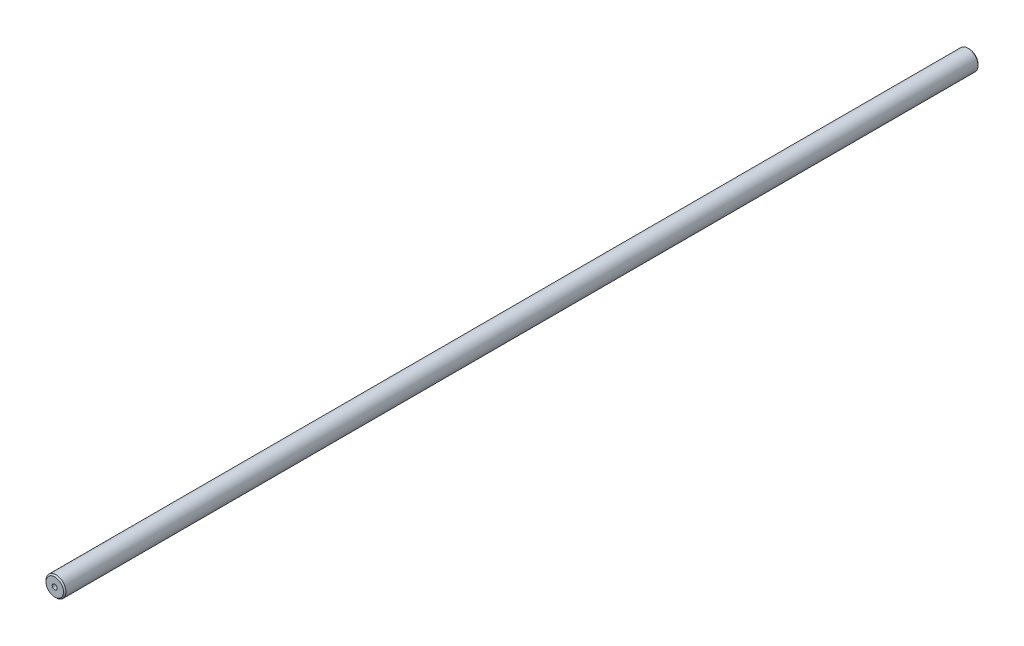
SolidWorks part; units mm, degrees
ref_plane "Front Plane" through (0, 0, 0) normal (0, 0, 1) x (1, 0, 0)
ref_plane "Top Plane" through (0, 0, 0) normal (0, 1, 0) x (1, 0, 0)
ref_plane "Right Plane" through (0, 0, 0) normal (1, 0, 0) x (0, 0, -1)
sketch "Sketch1" plane through (0, 0, 0) normal (0, 0, 1) x (1, 0, 0)
  circle A0 centre (0, 0) radius 4
  dimension "D1" = 8
extrude "Boss-Extrude1" add sketch "Sketch1" along normal blind 366
sketch "Sketch2" plane through (0, 0, 366) normal (0, 0, 1) x (1, 0, 0)
  circle A0 centre (0, 0) radius 1
  dimension "D1" = 2
extrude "Cut-Extrude1" cut sketch "Sketch2" against normal blind 10
chamfer "Chamfer1" distance 0.5 angle 45 2 edges at (4, 0, 0) (4, 0, 366)
